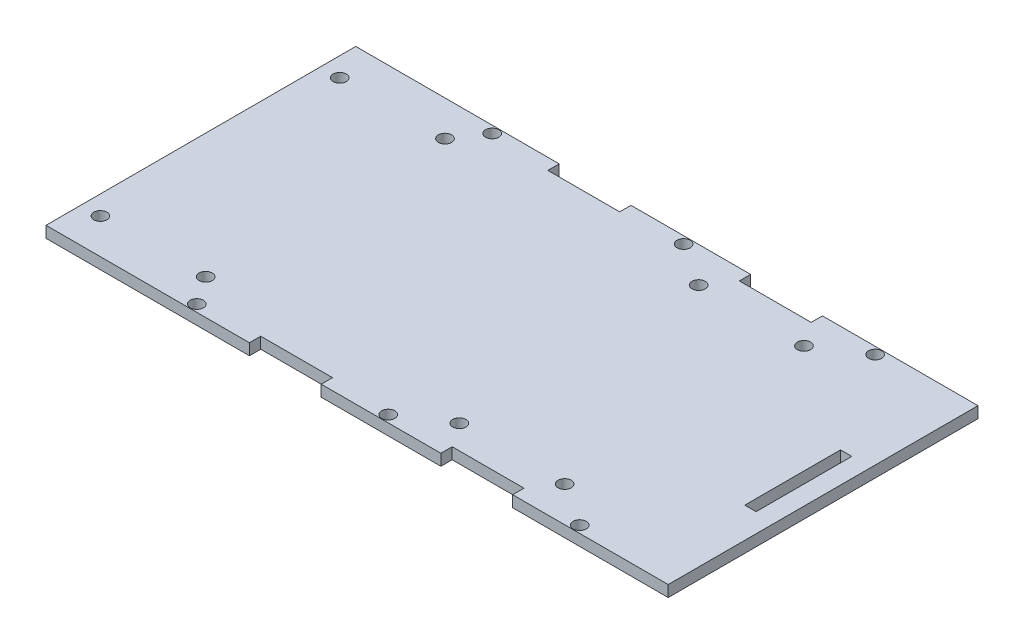
SolidWorks part; units mm, degrees
ref_plane "Front Plane" through (0, 0, 0) normal (0, 0, 1) x (1, 0, 0)
ref_plane "Top Plane" through (0, 0, 0) normal (0, 1, 0) x (1, 0, 0)
ref_plane "Right Plane" through (0, 0, 0) normal (1, 0, 0) x (0, 0, -1)
sketch "Sketch1" plane through (0, 0, 0) normal (0, 1, 0) x (1, 0, 0)
  line L1 (-114.3, 41.1) -> (-77.5289, 41.1)
  line L2 (-114.3, 41.1) -> (-114.3, -41.1)
  line L3 (-114.3, -41.1) -> (-77.5289, -41.1)
  line L4 (45.72, -12.7) -> (42.72, -12.7)
  line L5 (-74.8711, 41.1) -> (-60.325, 41.1)
  line L6 (26.7289, 41.1) -> (50.8, 41.1)
  line L7 (45.72, -12.7) -> (45.72, 12.7)
  line L8 (-24.0711, 41.1) -> (-9.525, 41.1)
  line L9 (-119.8539, 0) -> (200.76, 0) construction
  line L10 (45.72, 12.7) -> (42.72, 12.7)
  line L11 (26.7289, -41.1) -> (50.8, -41.1)
  line L12 (-24.0711, -41.1) -> (-9.525, -41.1)
  line L13 (-74.8711, -41.1) -> (-60.325, -41.1)
  line L14 (-41.275, -41.1) -> (-26.7289, -41.1)
  line L15 (9.525, -41.1) -> (24.0711, -41.1)
  line L16 (-60.325, -41.1) -> (-60.325, -38.1)
  line L17 (-60.325, -38.1) -> (-41.275, -38.1)
  line L18 (-41.275, -41.1) -> (-41.275, -38.1)
  line L19 (-60.325, -43.7685) -> (-41.275, -38.1) construction
  line L20 (-60.325, -38.1) -> (-41.275, -43.7685) construction
  line L21 (42.72, -12.7) -> (42.72, 12.7)
  line L22 (-9.525, -41.1) -> (-9.525, -38.1)
  line L23 (-9.525, -38.1) -> (9.525, -38.1)
  line L24 (9.525, -41.1) -> (9.525, -38.1)
  line L25 (-9.525, -43.7685) -> (9.525, -38.1) construction
  line L26 (-9.525, -38.1) -> (9.525, -43.7685) construction
  line L34 (-77.5289, -41.1) -> (-74.8711, -41.1)
  line L35 (9.525, 41.1) -> (9.525, 38.1)
  line L36 (-9.525, 38.1) -> (9.525, 38.1)
  line L37 (-9.525, 41.1) -> (-9.525, 38.1)
  line L38 (-41.275, 41.1) -> (-41.275, 38.1)
  line L39 (-60.325, 38.1) -> (-41.275, 38.1)
  line L40 (-60.325, 41.1) -> (-60.325, 38.1)
  line L41 (-41.275, 41.1) -> (-26.7289, 41.1)
  line L42 (9.525, 41.1) -> (24.0711, 41.1)
  line L45 (-77.5289, 41.1) -> (-74.8711, 41.1)
  line L46 (-26.7289, 41.1) -> (-24.0711, 41.1)
  line L47 (24.0711, 41.1) -> (26.7289, 41.1)
  line L51 (24.0711, -41.1) -> (26.7289, -41.1)
  line L52 (-26.7289, -41.1) -> (-24.0711, -41.1)
  line L53 (50.8, 41.1) -> (50.8, -41.1)
  circle A0 centre (-25.4, -39.195) radius 1.7526
  circle A2 centre (25.4, -39.195) radius 1.7526
  circle A5 centre (25.4, 39.195) radius 1.7526
  circle A6 centre (-25.4, 39.195) radius 1.7526
  circle A7 centre (-76.2, 39.195) radius 1.7526
  circle A9 centre (-76.2, -39.195) radius 1.7526
  point P34 (-50.8, -40.9342)
  point P39 (0, -40.9342)
  dimension "D5" = 5.08
  dimension "D6" = 3.5052
  dimension "D7" = 3.5052
  dimension "D15" = 1.905
  dimension "D8" = 3
  dimension "D2" = 114.3
  dimension "D3" = 25.4
  dimension "D4" = 28.4
  dimension "D9" = 19.05
  dimension "D10" = 19.05
  dimension "D12" = 3
  dimension "D13" = 3
  dimension "D16" = 1.905
  dimension "D17" = 1.905
  dimension "D19" = 165.1
extrude "Boss-Extrude1" add sketch "Sketch1" along normal blind 3
sketch "Sketch2" plane through (0, 3, 0) normal (0, 1, 0) x (1, 0, 0)
  line L0 (-114.3, -41.1) -> (-60.325, -41.1) construction
  line L1 (-114.3, 41.1) -> (-114.3, -41.1) construction
  line L2 (50.8, -41.1) -> (50.8, 41.1) construction
  circle A0 centre (-109.22, -31.75) radius 1.7526
  circle A1 centre (-81.28, -31.75) radius 1.7526
  circle A2 centre (13.97, -31.75) radius 1.7526
  circle A3 centre (-13.97, -31.75) radius 1.7526
  dimension "D1" = 3.5052
  dimension "D3" = 3.5052
  dimension "D6" = 36.83
  dimension "D7" = 3.5052
  dimension "D9" = 3.5052
  dimension "D2" = 9.35
  dimension "D4" = 27.94
  dimension "D5" = 5.08
  dimension "D8" = 27.94
extrude "Cut-Extrude1" cut sketch "Sketch2" against normal through all
mirror "Mirror1" about plane through (0, 0, 0) normal (0, 0, 1) of "Cut-Extrude1"
